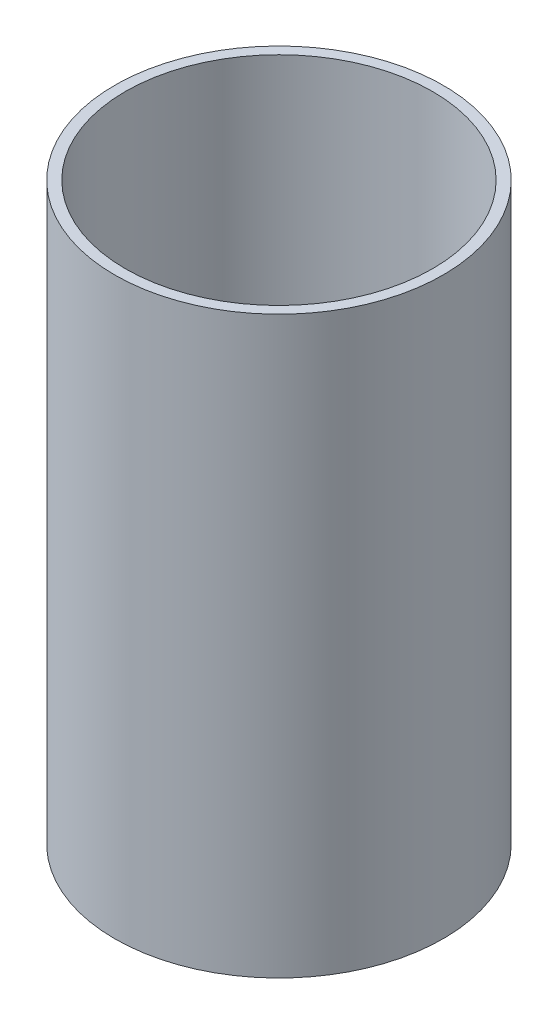
SolidWorks part; units mm, degrees
ref_plane "Front Plane" through (0, 0, 0) normal (0, 0, 1) x (1, 0, 0)
ref_plane "Top Plane" through (0, 0, 0) normal (0, 1, 0) x (1, 0, 0)
ref_plane "Right Plane" through (0, 0, 0) normal (1, 0, 0) x (0, 0, -1)
sketch "Sketch1" plane through (0, 0, 0) normal (0, 1, 0) x (1, 0, 0)
  circle A0 centre (0, 0) radius 23.749
  circle A1 centre (0, 0) radius 25.4
  dimension "D1" = 47.498
  dimension "D2" = 1.651
extrude "Boss-Extrude1" add sketch "Sketch1" along normal blind 88.9
